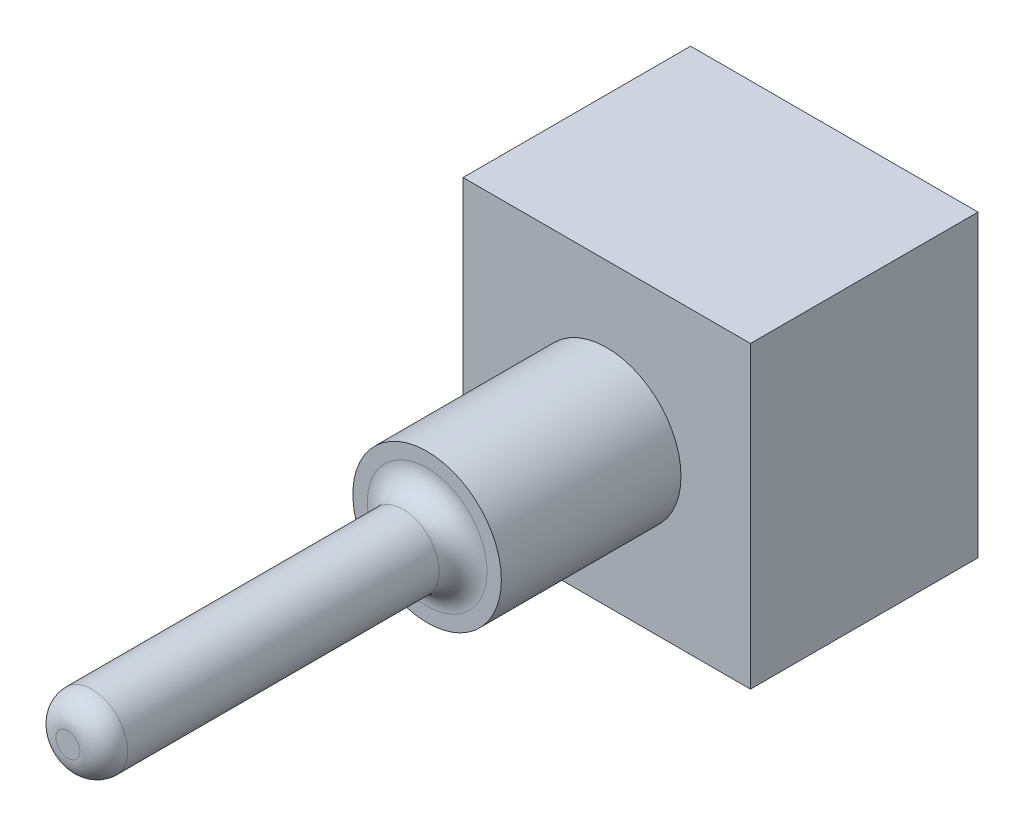
SolidWorks part; units mm, degrees
ref_plane "Plan de face" through (0, 0, 0) normal (0, 0, 1) x (1, 0, 0)
ref_plane "Plan de dessus" through (0, 0, 0) normal (0, 1, 0) x (1, 0, 0)
ref_plane "Plan de droite" through (0, 0, 0) normal (1, 0, 0) x (0, 0, -1)
sketch "Esquisse1" plane through (0, 0, 0) normal (0, 0, 1) x (1, 0, 0)
  line L1 (-63.8068, 29.1818) -> (-51.8068, 29.1818)
  line L2 (-63.8068, 29.1818) -> (-63.8068, 16.6818)
  line L3 (-63.8068, 16.6818) -> (-51.8068, 16.6818)
  line L4 (-51.8068, 29.1818) -> (-51.8068, 16.6818)
  dimension "D1" = 12
  dimension "D2" = 12.5
extrude "Boss.-Extru.1" add sketch "Esquisse1" along normal blind 9.5
sketch "Esquisse3" plane through (0, 0, 9.5) normal (0, 0, 1) x (1, 0, 0)
  line L0 (-51.8068, 16.6818) -> (-51.8068, 29.1818) construction
  line L1 (-63.8068, 16.6818) -> (-51.8068, 16.6818) construction
  circle A0 centre (-57.8068, 22.9318) radius 3.1
  point P2 (-51.8068, 22.9318)
  point P5 (-57.8068, 16.6818)
  dimension "D3" = 6.2
  dimension "D1" = 0
  dimension "D2" = 0
extrude "Boss.-Extru.2" add sketch "Esquisse3" along normal blind 7.5
sketch "Esquisse4" plane through (0, 0, 17) normal (0, 0, 1) x (1, 0, 0)
  circle A0 centre (-57.8068, 22.9318) radius 1.5
  circle A1 centre (-57.8068, 22.9318) radius 3.1 construction
  dimension "D2" = 3
  dimension "D1" = 0
extrude "Boss.-Extru.3" add sketch "Esquisse4" along normal blind 15
fillet "Congé3" radius 1 2 edges at (-56.3068, 22.9318, 17) (-56.3068, 22.9318, 32)
